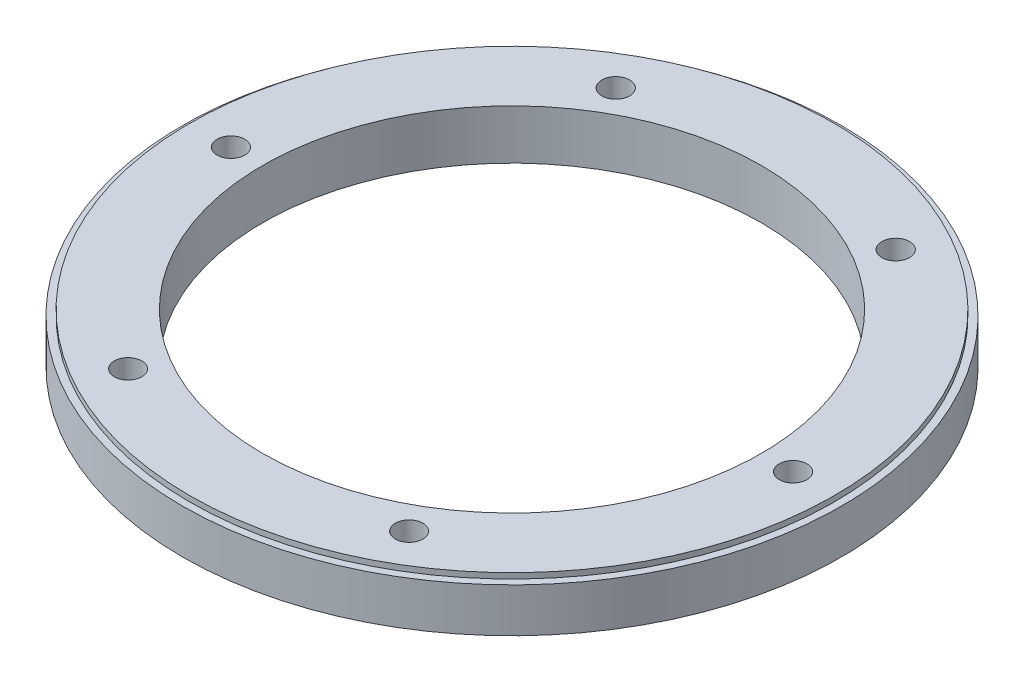
SolidWorks part; units mm, degrees
ref_plane "Front Plane" through (0, 0, 0) normal (0, 0, 1) x (1, 0, 0)
ref_plane "Top Plane" through (0, 0, 0) normal (0, 1, 0) x (1, 0, 0)
ref_plane "Right Plane" through (0, 0, 0) normal (1, 0, 0) x (0, 0, -1)
sketch "Sketch1" plane through (0, 0, 0) normal (0, 1, 0) x (1, 0, 0)
  circle A0 centre (0, 0) radius 75.946
  dimension "D1" = 151.892
extrude "Boss-Extrude1" add sketch "Sketch1" along normal blind 10.16
sketch "Sketch2" plane through (0, 10.16, 0) normal (0, 1, 0) x (1, 0, 0)
  line L0 (0, 63.5) -> (-52.8538, -35.1955)
  line L1 (-52.8538, -35.1955) -> (52.8538, -35.1955)
  line L2 (52.8538, -35.1955) -> (0, 63.5)
  circle A0 centre (0, 0) radius 75.946 construction
  dimension "D1" = 63.5
  dimension "D2" = 63.5
  dimension "D3" = 63.5
extrude "Cut-Extrude1" [suppressed] cut sketch "Sketch2" against normal blind 20.32
fillet "Fillet1" [suppressed] radius 2.54
sketch "Sketch3" [suppressed] plane through (0, 10.16, 0) normal (0, 1, 0) x (1, 0, 0)
  line L1 (33.8032, -46.5261) -> (54.6948, 17.7714)
  line L2 (54.6948, 17.7714) -> (0, 57.5095)
  line L3 (0, 57.5095) -> (-54.6948, 17.7714)
  line L4 (-54.6948, 17.7714) -> (-33.8032, -46.5261)
  line L5 (-33.8032, -46.5261) -> (33.8032, -46.5261)
  circle A0 centre (0, 0) radius 46.5261 construction
extrude "Cut-Extrude2" [suppressed] cut sketch "Sketch3" against normal blind 20.32
fillet "Fillet2" [suppressed] radius 2.54
sketch "Sketch4" [suppressed] plane through (0, 10.16, 0) normal (0, 1, 0) x (1, 0, 0)
  line L0 (0, 75.946) -> (0, -75.946) construction
  circle A0 centre (0, 0) radius 75.946 construction
  circle A1 centre (-23.8719, 55.6861) radius 3.175
  circle A2 centre (-50, -20.5139) radius 3.175
  circle A3 centre (23.8719, 55.6861) radius 3.175
  circle A4 centre (50, -20.5139) radius 3.175
  arc A5 (-53.2018, 18.8561) -> (-54.1245, 16.0163) centre (-51.7088, 16.8012) ccw construction
  point P16 (-54.1245, 17.5861)
  dimension "D1" = 6.35
  dimension "D2" = 6.35
  dimension "D3" = 76.2
  dimension "D4" = 38.1
  dimension "D5" = 100
extrude "Cut-Extrude3" [suppressed] cut sketch "Sketch4" against normal blind 20.32
sketch "Sketch7" plane through (0, 10.16, 0) normal (0, 1, 0) x (1, 0, 0)
  circle A0 centre (0, 0) radius 74.295
  dimension "D1" = 148.59
extrude "Boss-Extrude2" add sketch "Sketch7" along normal blind 1.27
sketch "Sketch6" plane through (0, 10.16, 0) normal (0, 1, 0) x (1, 0, 0)
  line L0 (0, 75.946) -> (0, -75.946) construction
  line L1 (-75.946, 0) -> (75.946, 0) construction
  line L2 (-37.8426, 65.8463) -> (38.0237, -65.7419) construction
  line L3 (-37.973, -65.7712) -> (37.973, 65.7712) construction
  circle A0 centre (0, 0) radius 75.946 construction
  circle A1 centre (-64.77, 0) radius 3.1835
  circle A2 centre (-32.2605, 56.1642) radius 3.2
  circle A3 centre (-32.385, -56.0925) radius 3.175
  circle A4 centre (32.385, -56.0925) radius 3.175
  circle A5 centre (64.77, 0) radius 3.1835
  circle A6 centre (32.2605, 56.1642) radius 3.2
  dimension "D1" = 6.4
  dimension "D2" = 6.35
  dimension "D3" = 64.77
  dimension "D4" = 64.77
  dimension "D5" = 64.77
extrude "Cut-Extrude5" cut sketch "Sketch6" against normal through all and the other way through all
sketch "Sketch9" plane through (0, 11.43, 0) normal (0, 1, 0) x (1, 0, 0)
  circle A1 centre (0, 0) radius 57.4675
  dimension "D1" = 114.935
extrude "Cut-Extrude7" cut sketch "Sketch9" against normal through all
